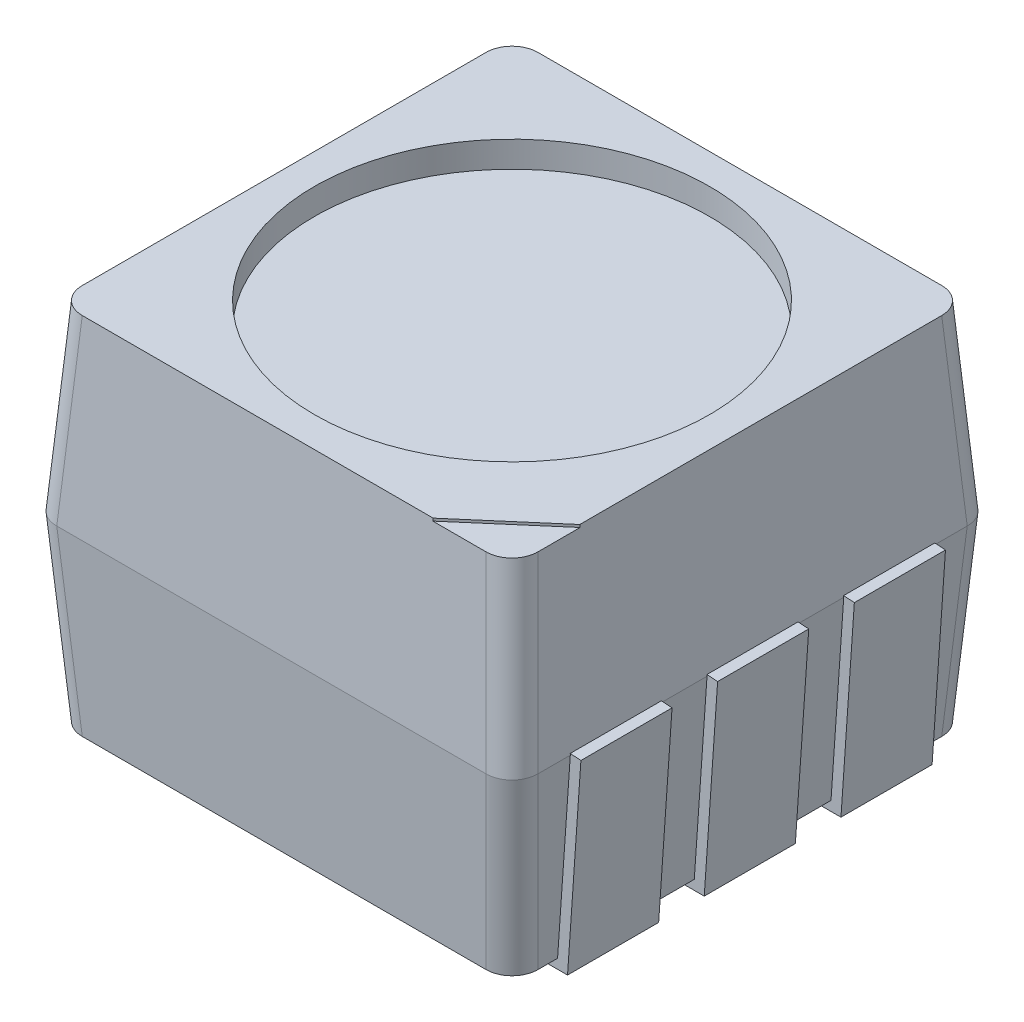
SolidWorks part; units mm, degrees
ref_plane "Front Plane" through (0, 0, 0) normal (0, 0, 1) x (1, 0, 0)
ref_plane "Top Plane" through (0, 0, 0) normal (0, 1, 0) x (1, 0, 0)
ref_plane "Right Plane" through (0, 0, 0) normal (1, 0, 0) x (0, 0, -1)
sketch "Sketch1" plane through (0, 0, 0) normal (0, 1, 0) x (1, 0, 0)
  line L1 (-1.75, 1.75) -> (1.75, 1.75)
  line L2 (-1.75, 1.75) -> (-1.75, -1.75)
  line L3 (-1.75, -1.75) -> (1.75, -1.75)
  line L4 (1.75, 1.75) -> (1.75, -1.75)
  line L5 (-1.75, 1.75) -> (1.75, -1.75) construction
  line L6 (-1.75, -1.75) -> (1.75, 1.75) construction
  point P0 (0, 0)
  dimension "D1" = 3.5
  dimension "D2" = 3.5
extrude "Boss-Extrude1" add sketch "Sketch1" along normal blind 1.4 draft 4 draft outward yes
sketch "Sketch2" plane through (0, 1.4, 0) normal (0, 1, 0) x (1, 0, 0)
  line L4 (1.8479, -1.8479) -> (1.8479, 1.8479)
  line L5 (1.8479, 1.8479) -> (-1.8479, 1.8479)
  line L6 (-1.8479, 1.8479) -> (-1.8479, -1.8479)
  line L7 (-1.8479, -1.8479) -> (1.8479, -1.8479)
  line L8 (1.8479, -1.8479) -> (1.8479, 1.8479)
  line L9 (1.8479, 1.8479) -> (-1.8479, 1.8479)
  line L10 (-1.8479, 1.8479) -> (-1.8479, -1.8479)
  line L11 (-1.8479, -1.8479) -> (1.8479, -1.8479)
  dimension "D1" = 0
extrude "Boss-Extrude2" add sketch "Sketch2" along normal blind 1.4 draft 4
fillet "Fillet1" radius 0.2 8 edges at (-1.7989, 0.7, -1.7989) (-1.7989, 2.1, -1.7989) (1.7989, 0.7, -1.7989) (1.7989, 2.1, -1.7989) (1.7989, 2.1, 1.7989) (1.7989, 0.7, 1.7989) (-1.7989, 2.1, 1.7989) (-1.7989, 0.7, 1.7989)
sketch "Sketch3" plane through (0, 2.8, 0) normal (0, 1, 0) x (1, 0, 0)
  circle A0 centre (0, 0) radius 1.5179
extrude "Cut-Extrude1" cut sketch "Sketch3" against normal blind 0.2
sketch "Sketch4" plane through (0, 0, 0) normal (0, 0, 1) x (1, 0, 0)
  line L0 (-1.9293, 1.4053) -> (-1.8264, -0.0735)
  line L1 (-1.8264, -0.0735) -> (-1.0764, -0.0735)
  dimension "D1" = 0.75
extrude "Extrude-Thin1" add sketch "Sketch4" along normal mid plane 0.7 thin thin type one direction reverse wall 0.2
pattern_linear "LPattern1" count 2 spacing 1.05 along (0, 0, 1) of "Extrude-Thin1"
pattern_linear "LPattern2" count 2 spacing 1.05 along (0, 0, -1) of "Extrude-Thin1"
mirror "Mirror1" about plane through (0, 0, 0) normal (1, 0, 0) of "LPattern1", "LPattern2", "Extrude-Thin1"
sketch "Sketch5" plane through (0, 2.8, 0) normal (0, 1, 0) x (1, 0, 0)
  line L0 (1.9918, -1.0212) -> (0.9408, -1.9253)
  line L1 (0.9408, -1.9253) -> (2.0286, -1.9253)
  line L2 (2.0286, -1.9253) -> (1.9918, -1.0212)
extrude "Cut-Extrude2" cut sketch "Sketch5" against normal blind 0.02
